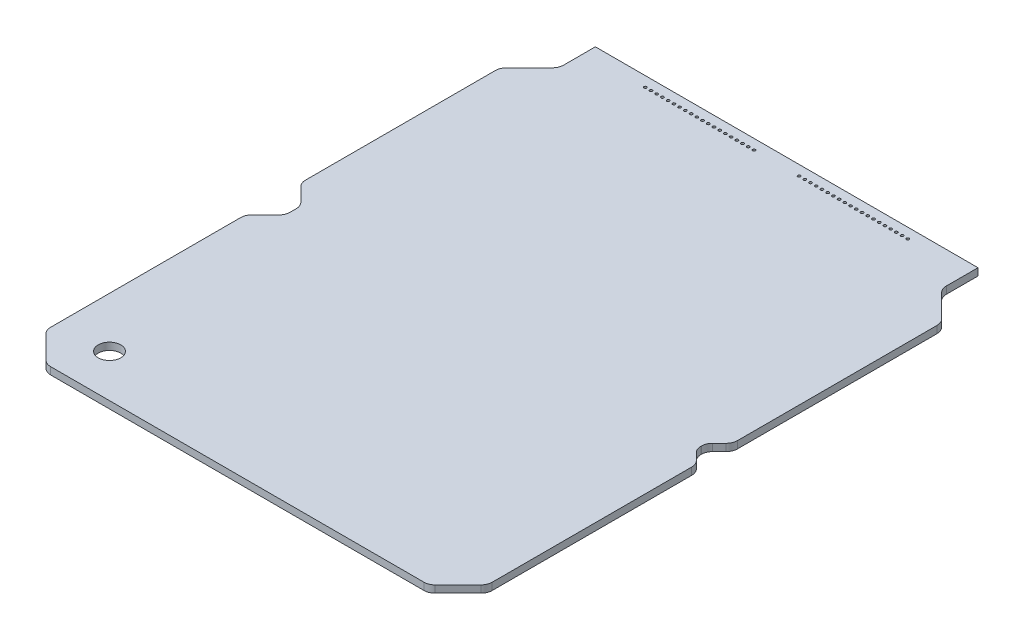
SolidWorks part; units mm, degrees
ref_plane "Front Plane" through (0, 0, 0) normal (0, 0, 1) x (1, 0, 0)
ref_plane "Top Plane" through (0, 0, 0) normal (0, 1, 0) x (1, 0, 0)
ref_plane "Right Plane" through (0, 0, 0) normal (1, 0, 0) x (0, 0, -1)
sketch "Sketch1" plane through (0, 0, 0) normal (0, 1, 0) x (1, 0, 0)
  line L0 (-42.4591, 0) -> (42.4591, 0)
  line L3 (-49, 6.5409) -> (-49, 50.7531)
  line L4 (-49, 50.7531) -> (-44.5287, 55.2244)
  line L5 (-44.5287, 55.2244) -> (-44.5287, 58.621)
  line L6 (-44.5287, 58.621) -> (-49, 63.0923)
  line L7 (-49, 63.0923) -> (-49, 107.3045)
  line L8 (-49, 107.3045) -> (-42.4591, 113.8454)
  line L9 (-42.4591, 121.9224) -> (42.4591, 121.9224)
  line L10 (-50, 54.1425) -> (-50, 3.1515) construction
  line L11 (-50, 59.7029) -> (-50, 116.2543) construction
  line L12 (0, 0) -> (0, 121.9224) construction
  line L13 (-45.7295, 3.2705) -> (-48.6287, 0.3713) construction
  line L14 (-48.6287, 56.9227) -> (-45.7295, 54.0236) construction
  line L15 (-48.6287, 56.9227) -> (-45.7295, 59.8218) construction
  line L16 (-45.7295, 110.5749) -> (-48.6287, 113.4741) construction
  line L17 (-42.4591, 113.8454) -> (-42.4591, 121.9224)
  line L18 (42.4591, 0) -> (49, 6.5409)
  line L19 (49, 6.5409) -> (49, 50.7531)
  line L20 (49, 50.7531) -> (44.5287, 55.2244) construction
  line L21 (44.5287, 55.2244) -> (44.5287, 58.621) construction
  line L22 (44.5287, 58.621) -> (49, 63.0923) construction
  line L23 (42.4591, 113.8454) -> (42.4591, 121.9224)
  line L24 (49, 107.3045) -> (42.4591, 113.8454)
  line L25 (49, 63.0923) -> (49, 107.3045)
  line L26 (-45.8485, -1) -> (-24.4481, -1) construction
  line L27 (-50, 3.1515) -> (-45.8485, -1) construction
  line L28 (-49, 6.5409) -> (-42.4591, 0)
  line L29 (50.0607, 51.8138) -> (46.0287, 55.8457)
  line L30 (46.0287, 55.8457) -> (46.0287, 57.9997)
  line L31 (46.0287, 57.9997) -> (50.0607, 62.0316)
  line L32 (49, 63.0923) -> (49, 60.971)
  line L33 (49, 50.7531) -> (49, 52.8744)
  circle A0 centre (-48.6287, 0.3713) radius 3.1 construction
  circle A1 centre (-48.6287, 56.9227) radius 3.1 construction
  circle A2 centre (-48.6287, 113.4741) radius 3.1 construction
  point P3 (-45.5287, 56.9227)
  point P4 (0, 0)
  point P27 (-46.4366, 2.5634)
  point P32 (-45.7295, 110.5749)
  dimension "D4" = 6.2
  dimension "D3" = 56.5514
  dimension "D5" = 56.5514
  dimension "D6" = 45.5287
  dimension "D7" = 50
  dimension "D1" = 8.4483
  dimension "D9" = 1
  dimension "D11" = 135
  dimension "D8" = 1
  dimension "D10" = 45
  dimension "D2" = 1
  dimension "D12" = 1
  dimension "D13" = 1.5
extrude "Boss-Extrude1" add sketch "Sketch1" along normal blind 1.6 contours L19 L33 L29 L30 L31 L32 L25 L24 L23 L9 L17 L8 L7 L6 L5 L4 L3 L28 L0 L18
fillet "Fillet1" radius 2.5 16 edges at (-49, 0.8, -6.5409) (-49, 0.8, -50.7531) (-44.5287, 0.8, -55.2244) (-44.5287, 0.8, -58.621) (-49, 0.8, -63.0923) (-49, 0.8, -107.3045) (-42.4591, 0.8, -113.8454) (42.4591, 0.8, -113.8454) (49, 0.8, -107.3045) (49, 0.8, -6.5409) (42.4591, 0.8, 0) (-42.4591, 0.8, 0) (49, 0.8, -52.8744) (46.0287, 0.8, -55.8457) (46.0287, 0.8, -57.9997) (49, 0.8, -60.971)
sketch "Sketch15" plane through (0, 1.6, 0) normal (0, 1, 0) x (1, 0, 0)
  line L2 (-44.8437, 16.4744) -> (-30.8483, 16.4744) construction
  line L3 (-44.8437, 16.4744) -> (-44.8437, 2.479) construction
  line L4 (-44.8437, 2.479) -> (-30.8483, 2.479) construction
  line L5 (-30.8483, 16.4744) -> (-30.8483, 2.479) construction
  line L6 (-41.4235, 0) -> (41.4235, 0) construction
  line L7 (-49, 7.5765) -> (-49, 49.7176) construction
  circle A0 centre (-37.846, 9.4767) radius 2.5
  point P9 (0, 0)
  point P10 (-37.846, 16.4744)
  point P11 (0, 0)
  point P12 (-44.8437, 9.4767)
  dimension "D2" = 5
  dimension "D1" = 2.479
  dimension "D3" = 13.9954
  dimension "D4" = 4.1563
extrude "Cut-Extrude5" cut sketch "Sketch15" against normal through all
sketch "Sketch16" plane through (0, 1.6, 0) normal (0, 1, 0) x (1, 0, 0)
  line L2 (-29.13, 119.6724) -> (-27.86, 119.6724) construction
  line L3 (5, 119.6724) -> (6.27, 119.6724) construction
  line L4 (-42.4591, 121.9224) -> (42.4591, 121.9224) construction
  circle A0 centre (-29.13, 119.6724) radius 0.3
  circle A1 centre (-27.86, 119.6724) radius 0.3
  circle A2 centre (-26.59, 119.6724) radius 0.3
  circle A3 centre (-25.32, 119.6724) radius 0.3
  circle A4 centre (-24.05, 119.6724) radius 0.3
  circle A5 centre (-22.78, 119.6724) radius 0.3
  circle A6 centre (-21.51, 119.6724) radius 0.3
  circle A7 centre (-20.24, 119.6724) radius 0.3
  circle A8 centre (-18.97, 119.6724) radius 0.3
  circle A9 centre (-17.7, 119.6724) radius 0.3
  circle A10 centre (-16.43, 119.6724) radius 0.3
  circle A11 centre (-15.16, 119.6724) radius 0.3
  circle A12 centre (-13.89, 119.6724) radius 0.3
  circle A13 centre (-12.62, 119.6724) radius 0.3
  circle A14 centre (-11.35, 119.6724) radius 0.3
  circle A15 centre (-10.08, 119.6724) radius 0.3
  circle A16 centre (-8.81, 119.6724) radius 0.3
  circle A17 centre (-7.54, 119.6724) radius 0.3
  circle A18 centre (-6.27, 119.6724) radius 0.3
  circle A19 centre (-5, 119.6724) radius 0.3
  circle A20 centre (5, 119.6724) radius 0.3
  circle A21 centre (6.27, 119.6724) radius 0.3
  circle A22 centre (7.54, 119.6724) radius 0.3
  circle A23 centre (8.81, 119.6724) radius 0.3
  circle A24 centre (10.08, 119.6724) radius 0.3
  circle A25 centre (11.35, 119.6724) radius 0.3
  circle A26 centre (12.62, 119.6724) radius 0.3
  circle A27 centre (13.89, 119.6724) radius 0.3
  circle A28 centre (15.16, 119.6724) radius 0.3
  circle A29 centre (16.43, 119.6724) radius 0.3
  circle A30 centre (17.7, 119.6724) radius 0.3
  circle A31 centre (18.97, 119.6724) radius 0.3
  circle A32 centre (20.24, 119.6724) radius 0.3
  circle A33 centre (21.51, 119.6724) radius 0.3
  circle A34 centre (22.78, 119.6724) radius 0.3
  circle A35 centre (24.05, 119.6724) radius 0.3
  circle A36 centre (25.32, 119.6724) radius 0.3
  circle A37 centre (26.59, 119.6724) radius 0.3
  circle A38 centre (27.86, 119.6724) radius 0.3
  circle A39 centre (29.13, 119.6724) radius 0.3
  point P5 (0, 0)
  dimension "D1" = 0.6
  dimension "D2" = 2.25
  dimension "D3" = 5
  dimension "D5" = 1.27
  dimension "D6" = 5
  dimension "D8" = 1.27
  dimension "D4" = 20
  dimension "D7" = 20
extrude "Cut-Extrude6" cut sketch "Sketch16" against normal through all
equation "\"D5@Sketch1\"=\"D3@Sketch1\""
